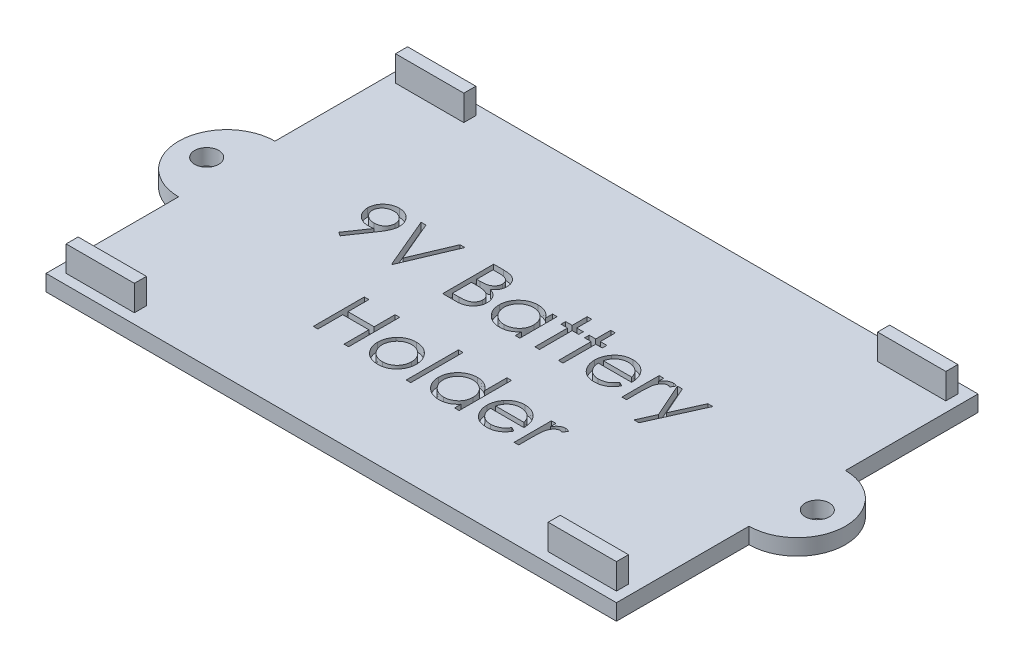
SolidWorks part; units mm, degrees
ref_plane "Front Plane" through (0, 0, 0) normal (0, 0, 1) x (1, 0, 0)
ref_plane "Top Plane" through (0, 0, 0) normal (0, 1, 0) x (1, 0, 0)
ref_plane "Right Plane" through (0, 0, 0) normal (1, 0, 0) x (0, 0, -1)
sketch "Sketch1" plane through (0, 0, 0) normal (0, 1, 0) x (1, 0, 0)
  line L1 (-35.5, -22.5) -> (35.5, -22.5)
  line L2 (-35.5, -22.5) -> (-35.5, 22.5)
  line L3 (-35.5, 22.5) -> (35.5, 22.5)
  line L4 (35.5, -22.5) -> (35.5, 22.5)
  line L5 (-35.5, -22.5) -> (35.5, 22.5) construction
  line L6 (-35.5, 22.5) -> (35.5, -22.5) construction
  point P0 (0, 0)
  dimension "D1" = 45
  dimension "D2" = 71
extrude "Boss-Extrude1" add sketch "Sketch1" along normal blind 2
sketch "Sketch2" plane through (0, 2, 0) normal (0, 1, 0) x (1, 0, 0)
  line L1 (-34.25, -21.25) -> (-25.75, -21.25)
  line L2 (-34.25, -21.25) -> (-34.25, -19.75)
  line L3 (-34.25, -19.75) -> (-25.75, -19.75)
  line L4 (-25.75, -21.25) -> (-25.75, -19.75)
  line L14 (-35.5, 22.5) -> (-35.5, -22.5) construction
  line L19 (-35.5, -22.5) -> (35.5, -22.5) construction
extrude "Boss-Extrude2" add sketch "Sketch2" along normal blind 3.175
mirror "Mirror1" about plane through (0, 0, 0) normal (0, 0, 1) of "Boss-Extrude2"
mirror "Mirror2" about plane through (0, 0, 0) normal (1, 0, 0) of "Mirror1", "Boss-Extrude2"
sketch "Sketch3" plane through (0, 2, 0) normal (0, 1, 0) x (1, 0, 0)
  line L0 (-35.5, 0) -> (35.5, 0) construction
  line L1 (-35.5, 22.5) -> (-35.5, -22.5) construction
  line L2 (35.5, -22.5) -> (35.5, 22.5) construction
  text T0 "9V Battery \r\nHolder" font "Century Gothic" height in points 24
extrude "Cut-Extrude1" cut sketch "Sketch3" against normal blind 1
sketch "Sketch4" plane through (0, 2, 0) normal (0, 1, 0) x (1, 0, 0)
  line L0 (-35.5, 22.5) -> (-35.5, -22.5) construction
  line L1 (-35.5, 6) -> (-35.5, -6)
  arc A0 (-35.5, 6) -> (-35.5, -6) centre (-35.5, 0) ccw
  dimension "D1" = 6
extrude "Boss-Extrude3" add sketch "Sketch4" against normal up to surface (2 mm away) up to face at (0, 0, 0)
sketch "Sketch5" plane through (0, 2, 0) normal (0, 1, 0) x (1, 0, 0)
  line L0 (-35.5, 22.5) -> (-35.5, 6) construction
  circle A0 centre (-38, 0) radius 1.5
extrude "Cut-Extrude2" cut sketch "Sketch5" against normal up to surface (2 mm away) up to face at (-12.8333, 0, 0)
mirror "Mirror3" about plane through (0, 0, 0) normal (1, 0, 0) of "Boss-Extrude3", "Cut-Extrude2"
equation "\"D4@Sketch2\"=\"D3@Sketch2\""
equation "\"Screw_Diameter\"=3"
equation "\"D1@Sketch5\"=\"Screw_Diameter\""
